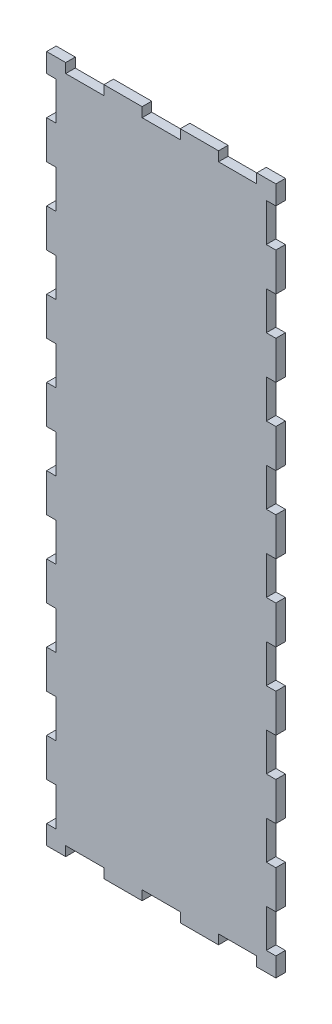
SolidWorks part; units mm, degrees
ref_plane "Front Plane" through (0, 0, 0) normal (0, 0, 1) x (1, 0, 0)
ref_plane "Top Plane" through (0, 0, 0) normal (0, 1, 0) x (1, 0, 0)
ref_plane "Right Plane" through (0, 0, 0) normal (1, 0, 0) x (0, 0, -1)
sketch "Sketch1" plane through (0, 0, 0) normal (0, 0, 1) x (1, 0, 0)
  line L1 (0, 0) -> (76.2, 0)
  line L2 (0, 0) -> (0, 228.6)
  line L3 (0, 228.6) -> (76.2, 228.6)
  line L4 (76.2, 0) -> (76.2, 228.6)
  dimension "D1" = 76.2
  dimension "D2" = 228.6
extrude "Extrude1" add sketch "Sketch1" along normal blind 3.175
sketch "Sketch3" plane through (0, 0, 3.175) normal (0, 0, 1) x (1, 0, 0)
  line L0 (76.2, 0) -> (76.2, 228.6) construction
  line L1 (76.2, 222.25) -> (73.025, 222.25)
  line L2 (76.2, 222.25) -> (76.2, 209.55)
  line L3 (76.2, 209.55) -> (73.025, 209.55)
  line L4 (73.025, 222.25) -> (73.025, 209.55)
  line L5 (76.2, 228.6) -> (0, 228.6) construction
  dimension "D1" = 3.175
  dimension "D2" = 12.7
  dimension "D3" = 6.35
extrude "Cut-Extrude1" cut sketch "Sketch3" against normal blind 3.175
pattern_linear "LPattern1" count 9 spacing 25.4 along (0, -1, 0) count 2 spacing 73.025 along (-1, 0, 0) of "Cut-Extrude1"
sketch "Sketch4" plane through (0, 0, 3.175) normal (0, 0, 1) x (1, 0, 0)
  line L0 (76.2, 228.6) -> (0, 228.6) construction
  line L1 (69.85, 228.6) -> (57.15, 228.6)
  line L2 (69.85, 228.6) -> (69.85, 225.425)
  line L3 (69.85, 225.425) -> (57.15, 225.425)
  line L4 (57.15, 228.6) -> (57.15, 225.425)
  dimension "D1" = 12.7
  dimension "D2" = 3.175
  dimension "D3" = 6.35
extrude "Cut-Extrude2" cut sketch "Sketch4" against normal blind 3.175
pattern_linear "LPattern2" count 3 spacing 25.4 along (-1, 0, 0) count 2 spacing 225.425 along (0, -1, 0) of "Cut-Extrude2"
